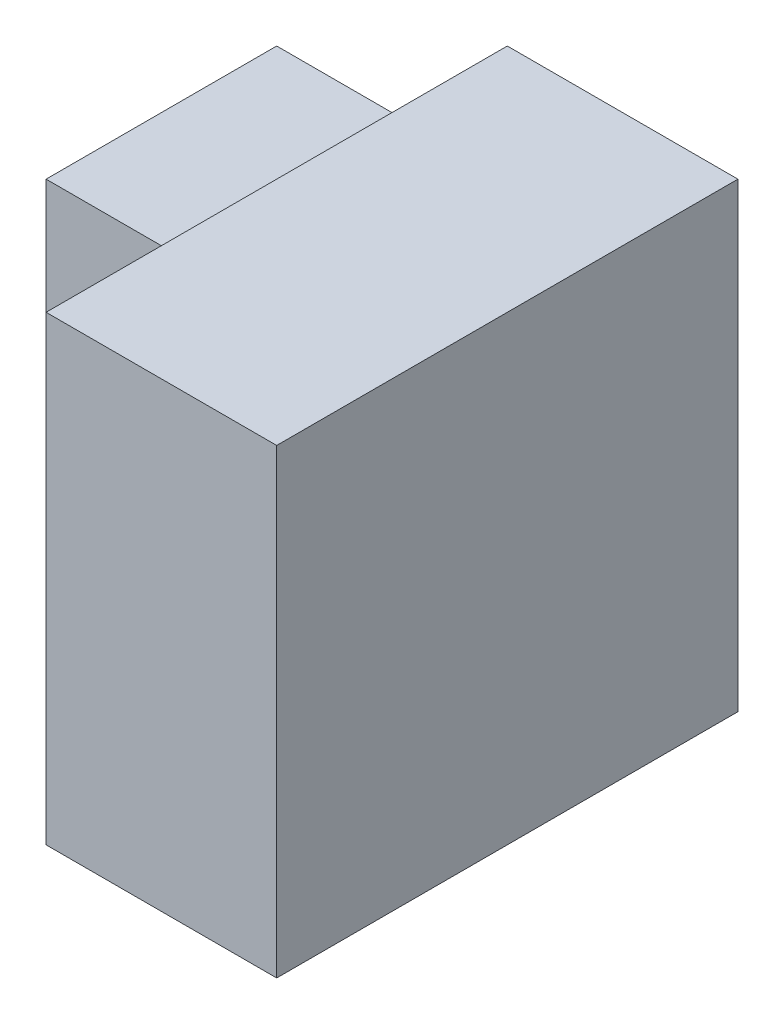
SolidWorks part; units mm, degrees
ref_plane "Front Plane" through (0, 0, 0) normal (0, 0, 1) x (1, 0, 0)
ref_plane "Top Plane" through (0, 0, 0) normal (0, 1, 0) x (1, 0, 0)
ref_plane "Right Plane" through (0, 0, 0) normal (1, 0, 0) x (0, 0, -1)
sketch "Sketch1" plane through (0, 0, 0) normal (1, 0, 0) x (0, 0, -1)
  line L1 (0, 0) -> (4, 0)
  line L2 (0, 0) -> (0, 4)
  line L3 (0, 4) -> (4, 4)
  line L4 (4, 0) -> (4, 4)
  dimension "D1" = 4
  dimension "D2" = 4
extrude "Boss-Extrude1" add sketch "Sketch1" along normal blind 2
sketch "Sketch2" plane through (0, 0, 0) normal (-1, 0, 0) x (0, 0, 1)
  line L1 (-4, 0) -> (-2, 0)
  line L2 (-4, 0) -> (-4, 3)
  line L3 (-4, 3) -> (-2, 3)
  line L4 (-2, 0) -> (-2, 3)
  dimension "D1" = 3
  dimension "D2" = 2
extrude "Boss-Extrude2" add sketch "Sketch2" along normal blind 2
sketch "Sketch3" plane through (-2, 0, 0) normal (-1, 0, 0) x (0, 0, 1)
  line L0 (-4, 3) -> (-2, 3)
  line L1 (-2, 3) -> (-2, 0)
  line L2 (-2, 0) -> (-4, 3)
  line M4 (-4, 3) -> (-4, 0)
  line M5 (-4, 0) -> (-2, 0)
extrude "Cut-Extrude1" cut sketch "Sketch3" against normal blind 2 contours L2 M5 M4
